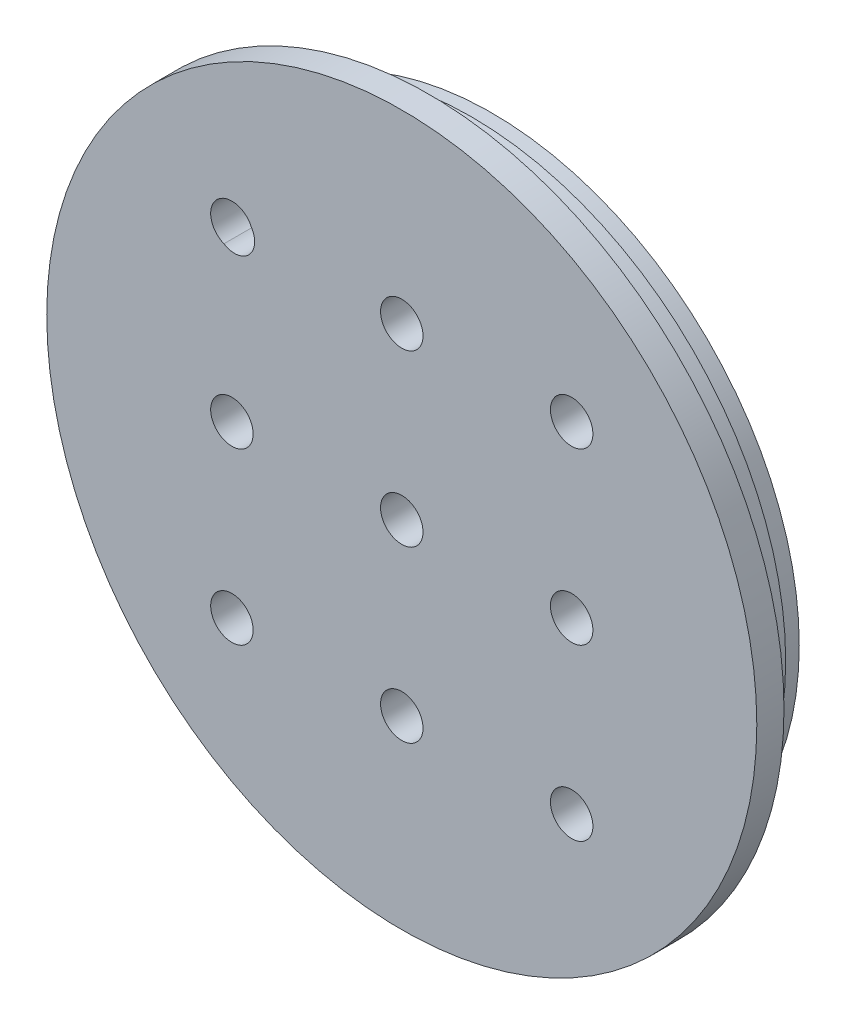
SolidWorks part; units mm, degrees
ref_plane "Front" through (0, 0, 0) normal (0, 0, 1) x (1, 0, 0)
ref_plane "Top" through (0, 0, 0) normal (0, 1, 0) x (1, 0, 0)
ref_plane "Right" through (0, 0, 0) normal (1, 0, 0) x (0, 0, -1)
sketch "Sketch2" plane through (0, 0, 0) normal (0, 0, 1) x (1, 0, 0)
  line L0 (-63.5, 63.5) -> (63.5, -63.5) construction
  line L1 (-63.5, 63.5) -> (63.5, 63.5)
  line L2 (-63.5, 63.5) -> (-63.5, -63.5)
  line L3 (-63.5, -63.5) -> (63.5, -63.5)
  line L4 (63.5, 63.5) -> (63.5, -63.5)
  dimension "D1" = 127
  dimension "D2" = 127
extrude "HOUSING" add sketch "Sketch2" along normal blind 39.5
sketch "Sketch3" plane through (0, 0, 39.5) normal (0, 0, 1) x (1, 0, 0)
  circle A0 centre (0, 0) radius 19.05
  dimension "D1" = 38.1
extrude "Cut-Extrude1" cut sketch "Sketch3" against normal through all
sketch "Sketch4" plane through (0, 0, 39.5) normal (0, 0, 1) x (1, 0, 0)
  circle A0 centre (0, 0) radius 45.974
  dimension "D1" = 91.948
extrude "Cut-Extrude2" cut sketch "Sketch4" against normal blind 4.698 flip side to cut
sketch "Sketch8" plane through (0, 0, 34.802) normal (0, 0, 1) x (1, 0, 0)
  line L0 (3.048, -63.5) -> (3.048, -57.528)
  line L1 (-63.5, -63.5) -> (63.5, -63.5) construction
  line L2 (7.2207, -51.5629) -> (45.3207, -37.6564)
  line L3 (53.848, -43.6215) -> (53.848, -63.5)
  line L4 (-63.5, 63.5) -> (-63.5, -63.5) construction
  line L5 (3.048, -63.5) -> (53.848, -63.5)
  line L6 (0, 0) -> (83.0961, 0) construction
  line L7 (3.048, 63.5) -> (53.848, 63.5)
  line L8 (53.848, 43.6215) -> (53.848, 63.5)
  line L9 (7.2207, 51.5629) -> (45.3207, 37.6564)
  line L10 (3.048, 63.5) -> (3.048, 57.528)
  line L11 (53.848, -51.1628) -> (53.848, -17.132) construction
  line L12 (3.048, -53.086) -> (67.489, -29.5651) construction
  line L13 (3.048, -61.8074) -> (3.048, -48.2133) construction
  arc A0 (3.048, -57.528) -> (7.2207, -51.5629) centre (9.398, -57.528) cw
  arc A1 (45.3207, -37.6564) -> (53.848, -43.6215) centre (47.498, -43.6215) cw
  arc A2 (45.3207, 37.6564) -> (53.848, 43.6215) centre (47.498, 43.6215) ccw
  arc A3 (3.048, 57.528) -> (7.2207, 51.5629) centre (9.398, 57.528) ccw
  point P27 (53.848, -34.544)
  point P30 (3.048, -53.086)
  dimension "D1" = 6.35
  dimension "D2" = 50.8
  dimension "D3" = 66.548
  dimension "D4" = 28.956
  dimension "D5" = 10.414
extrude "MOUNTING POCKETS" cut sketch "Sketch8" against normal blind 24.384
sketch "Sketch21" plane through (63.5, -23.6461, 1.1666) normal (1, 0, 0) x (0, 0, -1)
  line L0 (1.1666, 111.3134) -> (1.1666, 5.23) construction
  line L1 (-54.2716, 23.6461) -> (63.3306, 23.6461) construction
  line L2 (-20.6415, 75.2421) -> (-21.0415, 76.0421)
  line L3 (-27.0254, 72.0502) -> (-27.4254, 72.8502)
  line L4 (1.1666, -39.8539) -> (1.1666, 87.1461) construction
  line L5 (-27.0254, -24.7579) -> (-27.4254, -25.5579)
  line L6 (-20.6415, -27.9498) -> (-21.0415, -28.7498)
  arc A0 (-21.0415, 76.0421) -> (-27.4254, 72.8502) centre (-24.2334, 74.4461) ccw
  arc A1 (-27.0254, 72.0502) -> (-20.6415, 75.2421) centre (-23.8334, 73.6461) ccw
  arc A2 (-27.0254, -24.7579) -> (-20.6415, -27.9498) centre (-23.8334, -26.3539) cw
  arc A3 (-21.0415, -28.7498) -> (-27.4254, -25.5579) centre (-24.2334, -27.1539) cw
  dimension "HORIZ METRIC DIST" = 25
  dimension "HORIZ ENG DIST" = 25.4
  dimension "VERTICAL METRIC DIST" = 50
  dimension "VERT ENG DIST" = 50.8
extrude "ENG_METRIC SLOT VERTICAL" cut sketch "Sketch21" against normal up to next
sketch "Sketch212" plane through (34.0621, -104.656, 0) normal (0, 0, -1) x (-1, 0, 0)
  line L0 (34.0621, 192.3232) -> (34.0621, 86.2399) construction
  line L1 (-54.2716, 104.656) -> (63.3306, 104.656) construction
  line L2 (12.254, 156.252) -> (11.854, 157.052)
  line L3 (5.8701, 153.06) -> (5.4701, 153.86)
  line L4 (5.8701, 56.252) -> (5.4701, 55.452)
  line L5 (12.254, 53.06) -> (11.854, 52.26)
  arc A0 (11.854, 157.052) -> (5.4701, 153.86) centre (8.6621, 155.456) ccw
  arc A1 (5.8701, 153.06) -> (12.254, 156.252) centre (9.0621, 154.656) ccw
  arc A2 (5.8701, 56.252) -> (12.254, 53.06) centre (9.0621, 54.656) cw
  arc A3 (11.854, 52.26) -> (5.4701, 55.452) centre (8.6621, 53.856) cw
  dimension "HORIZ METRIC DIST" = 25
  dimension "HORIZ ENG DIST" = 25.4
  dimension "VERTICAL METRIC DIST" = 50
  dimension "VERT ENG DIST" = 50.8
extrude "ENG_METRIC SLOT HORIZONTAL" cut sketch "Sketch212" against normal through all
fillet "Fillet3" radius 0.508 10 edges at (53.848, 53.5608, 10.418) (51.1378, 38.4182, 10.418) (26.2707, 44.6097, 10.418) (4.1947, 53.8882, 10.418) (3.048, 60.514, 10.418) (53.848, -53.5608, 10.418) (51.1378, -38.4182, 10.418) (26.2707, -44.6097, 10.418) (4.1947, -53.8882, 10.418) (3.048, -60.514, 10.418)
hole_wizard "#10-32 Tapped Hole1" positions "Sketch221" profile "Sketch220" tap size "#10-32" standard "Ansi Inch"
sketch "Sketch221" plane through (0, 0, 39.5) normal (0, 0, 1) x (1, 0, 0)
  line L0 (7.4019, 0) -> (-7.4019, 0) construction
  line L1 (0, -7.4019) -> (0, 7.4019) construction
  line L2 (0, 0) -> (26.9875, 0) construction
  line L3 (0, 0) -> (0, 26.3763) construction
  point P0 (26.9875, -26.9875)
  point P9 (26.9875, 26.9875)
  point P10 (-26.9875, 26.9875)
  point P11 (-26.9875, -26.9875)
  dimension "D1" = 26.9875
  dimension "D2" = 26.9875
sketch "Sketch220" plane through (26.9875, -26.9875, 39.5) normal (1, 0, 0) x (0, -1, 0)
  line L0 (0, 0) -> (0, 13.2428)
  line L1 (0, 13.2428) -> (2.0193, 12.0294)
  line L2 (2.0193, 12.0294) -> (2.0193, 0)
  line L5 (2.0193, 0) -> (0, 0)
  line L10 (0, 13.2428) -> (-2.0193, 12.0294) construction
  line L11 (0, -6.35) -> (0, 107.95) construction
  dimension "Tap Drill Dia." = 4.0386
  dimension "Tap Drill Depth" = 12.0294
  dimension "Drill Angle" = 118
ref_plane "Plane1" through (0, 0, 48.26) normal (0, 0, 1) x (1, 0, 0)
sketch "Sketch219" plane through (0, 0, 48.26) normal (0, 0, 1) x (1, 0, 0)
  circle A0 centre (0, 0) radius 53.086
  dimension "D1" = 106.172
extrude "Extrude2" add sketch "Sketch219" against normal blind 10.414
sketch "Sketch222" plane through (0, 0, 37.846) normal (0, 0, -1) x (-1, 0, 0)
  circle A0 centre (0, 0) radius 46.99
  dimension "D1" = 93.98
extrude "Cut-Extrude6" cut sketch "Sketch222" against normal blind 6.35
hole_wizard "1/4-20 Tapped Hole2" positions "Sketch231" profile "Sketch230" tap size "1/4-20" standard "Ansi Inch"
sketch "Sketch231" plane through (0, 0, 48.26) normal (0, 0, 1) x (1, 0, 0)
  line L0 (0, -7.4019) -> (0, 7.4019) construction
  line L1 (7.4019, 0) -> (-7.4019, 0) construction
  point P0 (-25.4, 25.4)
  dimension "D1" = 25.4
  dimension "D2" = 25.4
sketch "Sketch230" plane through (-25.4, 25.4, 48.26) normal (1, 0, 0) x (0, -1, 0)
  line L0 (0, 0) -> (0, 9.5338)
  line L1 (0, 9.5338) -> (2.5527, 8)
  line L2 (2.5527, 8) -> (2.5527, 6)
  line L3 (2.5527, 6) -> (3.175, 6)
  line L4 (3.175, 6) -> (3.175, 0)
  line L5 (3.175, 0) -> (0, 0)
  line L10 (0, 9.5338) -> (-2.5527, 8) construction
  line L11 (0, -6.35) -> (0, 107.95) construction
  dimension "Tap Drill Dia." = 5.1054
  dimension "Tap Drill Depth" = 8
  dimension "Thread Major Dia." = 6.35
  dimension "Thread Depth" = 6
  dimension "Drill Angle" = 118
pattern_linear "LPattern14" count 3 spacing 25.4 along (1, 0, 0) count 3 spacing 25.4 along (0, -1, 0) of "1/4-20 Tapped Hole2"
sketch "Sketch226" plane through (0, 0, 48.26) normal (0, 0, 1) x (1, 0, 0)
  circle A0 centre (0, 0) radius 19.05
  dimension "D1" = 38.1
extrude "Cut-Extrude7" [suppressed] cut sketch "Sketch226" against normal up to next
hole_wizard "M6x1.0 Tapped Hole1" positions "Sketch233" profile "Sketch232" tap size "M6x1.0" standard "Ansi Metric"
sketch "Sketch233" plane through (0, 0, 48.26) normal (0, 0, 1) x (1, 0, 0)
  line L0 (0, -7.4019) -> (0, 7.4019) construction
  line L1 (7.4019, 0) -> (-7.4019, 0) construction
  point P0 (-25, 25)
  dimension "D1" = 25
  dimension "D2" = 25
sketch "Sketch232" plane through (-25, 25, 48.26) normal (1, 0, 0) x (0, -1, 0)
  line L0 (0, 0) -> (0, 9.5022)
  line L1 (0, 9.5022) -> (2.5, 8)
  line L2 (2.5, 8) -> (2.5, 6)
  line L3 (2.5, 6) -> (3, 6)
  line L4 (3, 6) -> (3, 0)
  line L5 (3, 0) -> (0, 0)
  line L10 (0, 9.5022) -> (-2.5, 8) construction
  line L11 (0, -6.35) -> (0, 107.95) construction
  dimension "Tap Drill Dia." = 5
  dimension "Tap Drill Depth" = 8
  dimension "Thread Major Dia." = 6
  dimension "Thread Depth" = 6
  dimension "Drill Angle" = 118
pattern_linear "LPattern16" [suppressed] count 3 spacing 25 count 3 spacing 25
sketch "Sketch234" plane through (-63.5, 0, 0) normal (-1, 0, 0) x (0, 0, 1)
  line L1 (34.802, 63.5) -> (0, 63.5)
  line L2 (34.802, 63.5) -> (34.802, -63.5)
  line L3 (34.802, -63.5) -> (0, -63.5)
  line L4 (0, 63.5) -> (0, -63.5)
extrude "Cut-Extrude8" cut sketch "Sketch234" against normal through all
